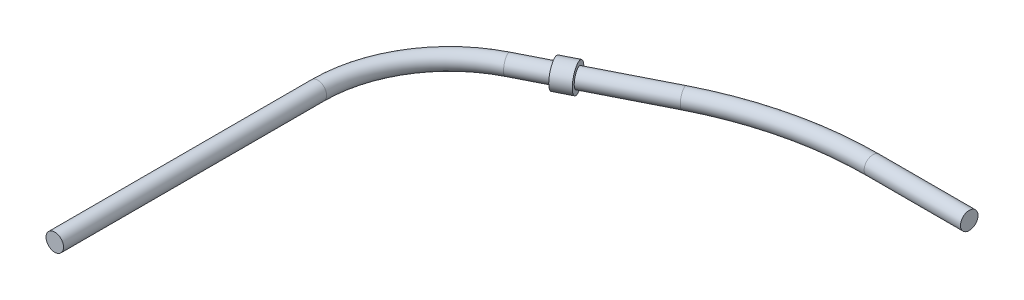
SolidWorks part; units mm, degrees
ref_plane "Front Plane" through (0, 0, 0) normal (0, 0, 1) x (1, 0, 0)
ref_plane "Top Plane" through (0, 0, 0) normal (0, 1, 0) x (1, 0, 0)
ref_plane "Right Plane" through (0, 0, 0) normal (1, 0, 0) x (0, 0, -1)
sketch "Esquisse1" plane through (0, 0, 0) normal (0, 1, 0) x (1, 0, 0)
  line L0 (0, 0) -> (0, 30)
  line L1 (8.2366, 43.3887) -> (21.6253, 50.152)
  line L2 (39.0146, 54.2949) -> (50, 54.2949)
  arc A0 (0, 30) -> (8.2366, 43.3887) centre (15, 30) cw
  arc A1 (21.6253, 50.152) -> (39.0146, 54.2949) centre (39.0146, 15.7284) cw
  dimension "D2" = 15
  dimension "D5" = 61.5455
  dimension "D1" = 30
  dimension "D3" = 15
  dimension "D4" = 50
sketch "Esquisse2" plane through (0, 0, 0) normal (0, 0, 1) x (1, 0, 0)
  circle A0 centre (0, 0) radius 1
sweep "Balayage1" add profiles "Esquisse2" path "Esquisse1"
surface "Surface-Plan1"
ref_plane "Plan3" through (28.487, 0, -14.3904) normal (-0.8926, 0, 0.4509) x (0.4509, 0, 0.8926)
sketch "Esquisse3" plane through (28.487, 0, -14.3904) normal (-0.8926, 0, 0.4509) x (0.4509, 0, 0.8926)
  circle A0 centre (-35.014, 0) radius 1
extrude "Extru.-Mince1" add sketch "Esquisse3" along normal mid plane 2 thin contours A0
